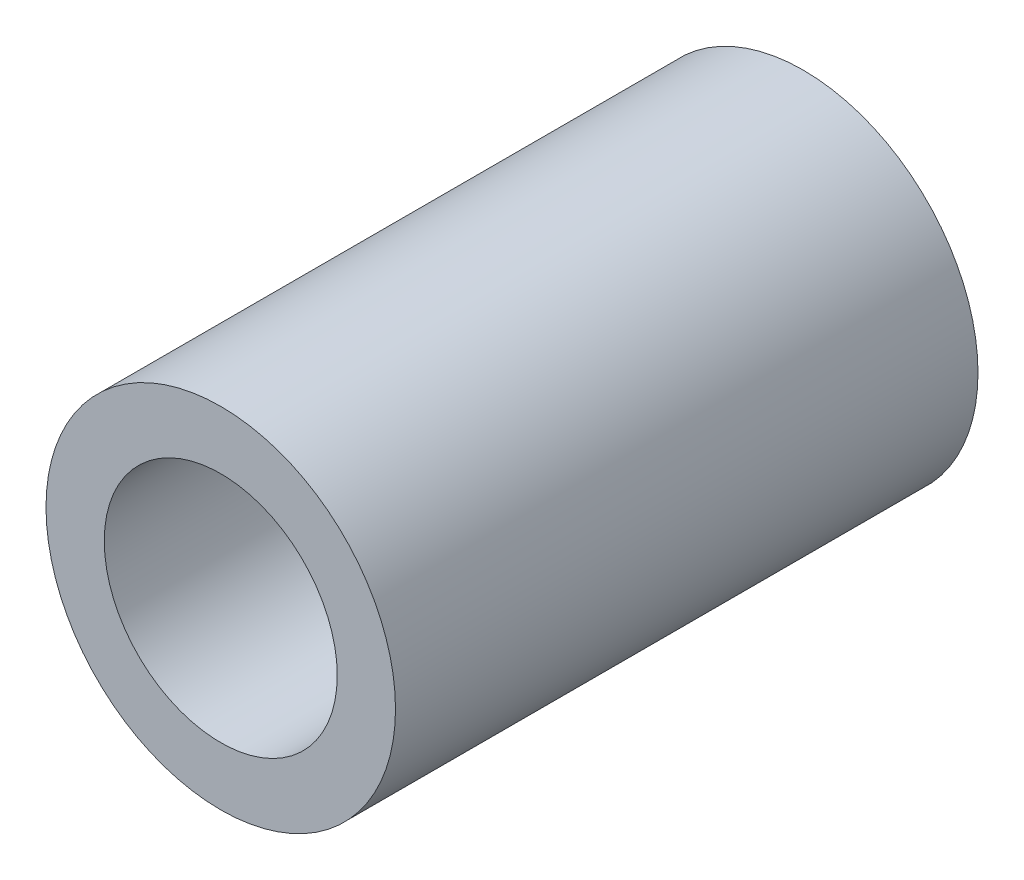
SolidWorks part; units mm, degrees
ref_plane "Plan de face" through (0, 0, 0) normal (0, 0, 1) x (1, 0, 0)
ref_plane "Plan de dessus" through (0, 0, 0) normal (0, 1, 0) x (1, 0, 0)
ref_plane "Plan de droite" through (0, 0, 0) normal (1, 0, 0) x (0, 0, -1)
sketch "Esquisse1" plane through (0, 0, 0) normal (0, 0, 1) x (1, 0, 0)
  circle A0 centre (0, 0) radius 3
  circle A1 centre (0, 0) radius 2
extrude "Extrusion1" add sketch "Esquisse1" along normal blind 10
